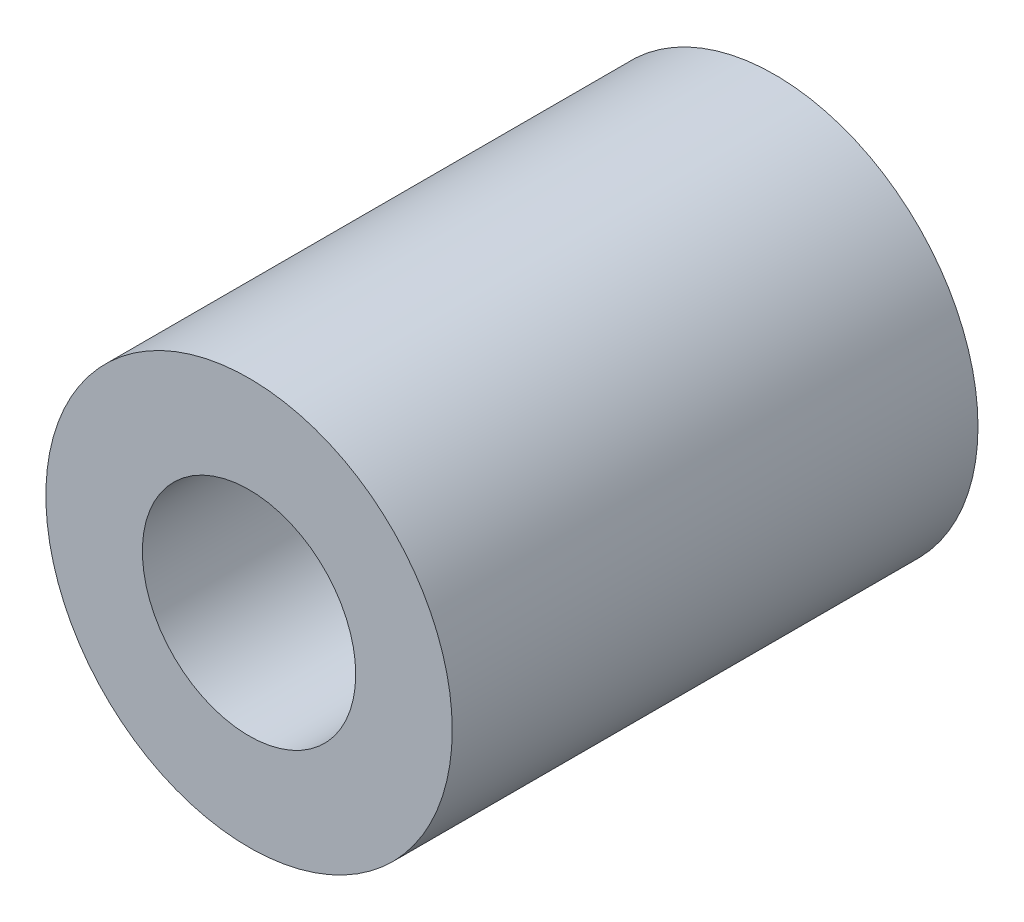
SolidWorks part; units mm, degrees
ref_plane "正面" through (0, 0, 0) normal (0, 0, 1) x (1, 0, 0)
ref_plane "平面" through (0, 0, 0) normal (0, 1, 0) x (1, 0, 0)
ref_plane "右側面" through (0, 0, 0) normal (1, 0, 0) x (0, 0, -1)
sketch "ｽｹｯﾁ1" plane through (0, 0, 0) normal (0, 0, 1) x (1, 0, 0)
  circle A0 centre (0, 0) radius 2.1
  circle A1 centre (0, 0) radius 4
  dimension "D1" = 4.2
  dimension "D2" = 8
extrude "ﾎﾞｽ - 押し出し1" add sketch "ｽｹｯﾁ1" along normal blind 10.35
